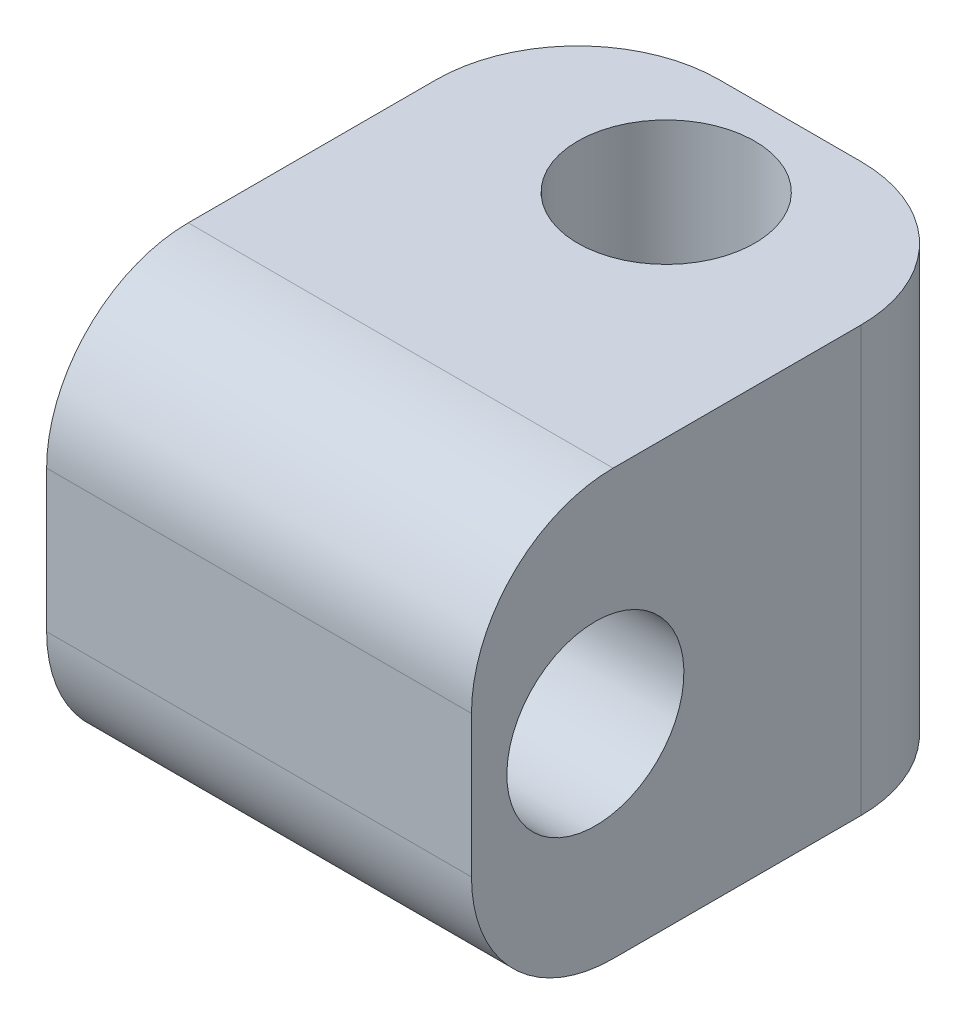
SolidWorks part; units mm, degrees
ref_plane "Front Plane" through (0, 0, 0) normal (0, 0, 1) x (1, 0, 0)
ref_plane "Top Plane" through (0, 0, 0) normal (0, 1, 0) x (1, 0, 0)
ref_plane "Right Plane" through (0, 0, 0) normal (1, 0, 0) x (0, 0, -1)
sketch "Sketch1" plane through (0, 0, 0) normal (0, 0, 1) x (1, 0, 0)
  line L0 (0, 6) -> (0, 0) construction
  line L1 (-6, 6) -> (6, 6)
  line L2 (-6, 6) -> (-6, -6)
  line L3 (-6, -6) -> (6, -6)
  line L4 (6, 6) -> (6, -6)
  line L5 (0, 0) -> (6, 0) construction
  dimension "D1" = 12
extrude "Extrude1" add sketch "Sketch1" along normal mid plane 15
sketch "Sketch2" plane through (0, 6, 0) normal (0, 1, 0) x (1, 0, 0)
  line L0 (0, 4) -> (0, 0) construction
  circle A0 centre (0, 4) radius 2.5
  dimension "D1" = 5
  dimension "D2" = 4
extrude "Cut-Extrude1" cut sketch "Sketch2" against normal through all
sketch "Sketch3" plane through (6, 0, 0) normal (1, 0, 0) x (0, 0, -1)
  line L0 (0, 0) -> (-4, 0) construction
  circle A0 centre (-4, 0) radius 2.5
  dimension "D2" = 5
  dimension "D1" = 4
extrude "Cut-Extrude2" cut sketch "Sketch3" against normal through all
fillet "Fillet1" radius 4 4 edges at (-6, 0, -7.5) (6, 0, -7.5) (0, -6, 7.5) (0, 6, 7.5)
